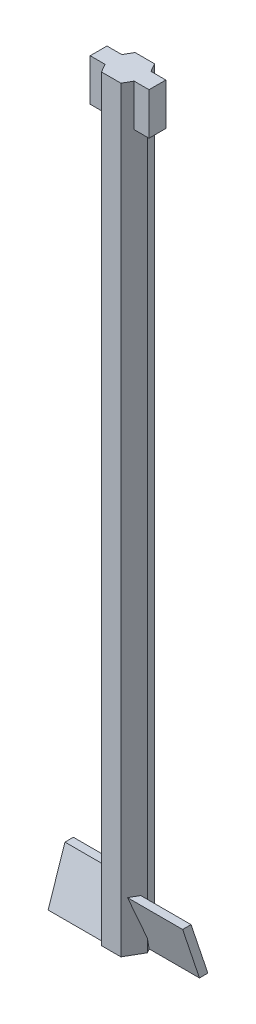
SolidWorks part; units mm, degrees
ref_plane "Front Plane" through (0, 0, 0) normal (0, 0, 1) x (1, 0, 0)
ref_plane "Top Plane" through (0, 0, 0) normal (0, 1, 0) x (1, 0, 0)
ref_plane "Right Plane" through (0, 0, 0) normal (1, 0, 0) x (0, 0, -1)
sketch "Sketch1" plane through (0, 0, 0) normal (0, 1, 0) x (1, 0, 0)
  line L1 (-1.1547, 2) -> (-2.3094, 0)
  line L2 (-2.3094, 0) -> (-1.1547, -2)
  line L3 (-1.1547, -2) -> (1.1547, -2)
  line L4 (1.1547, -2) -> (2.3094, 0)
  line L5 (2.3094, 0) -> (1.1547, 2)
  line L6 (1.1547, 2) -> (-1.1547, 2)
  circle A1 centre (0, 0) radius 2 construction
extrude "Boss-Extrude1" add sketch "Sketch1" along normal blind 90
sketch "Sketch2" plane through (0, 90, 0) normal (0, 1, 0) x (1, 0, 0)
  line L1 (-3.5, 1) -> (3.5, 1)
  line L2 (-3.5, 1) -> (-3.5, -1)
  line L3 (-3.5, -1) -> (3.5, -1)
  line L4 (3.5, 1) -> (3.5, -1)
  line L5 (-3.5, 1) -> (3.5, -1) construction
  line L6 (-3.5, -1) -> (3.5, 1) construction
  point P0 (0, 0)
  dimension "D1" = 2
  dimension "D2" = 7
extrude "Boss-Extrude2" add sketch "Sketch2" against normal blind 5
sketch "Sketch3" plane through (0, 0, 0) normal (1, 0, 0) x (0, 0, -1)
  line L0 (-1.5, 6) -> (-0.5, 6)
  line L2 (1.5, 0) -> (0.5, 0)
  line L4 (-1.5, 6) -> (0.5, 0)
  line L5 (-0.5, 6) -> (1.5, 0)
  dimension "D1" = 1
  dimension "D2" = 1
  dimension "D3" = 6
extrude "Boss-Extrude3" add sketch "Sketch3" along normal blind 8
sketch "Sketch4" plane through (0, 0, 0) normal (1, 0, 0) x (0, 0, -1)
  line L0 (1.5, 6) -> (0.5, 6)
  line L4 (-1.5, 0) -> (-0.5, 0)
  line L5 (1.5, 6) -> (-0.5, 0)
  line L6 (0.5, 6) -> (-1.5, 0)
  point P4 (0, 0)
  point P5 (0, 0)
  dimension "D1" = 1
  dimension "D2" = 6
  dimension "D3" = 1
extrude "Boss-Extrude4" add sketch "Sketch4" against normal blind 8
ref_plane "Plane1" through (0, 0, 0) normal (1, 0, 0) x (0, 0, -1)
